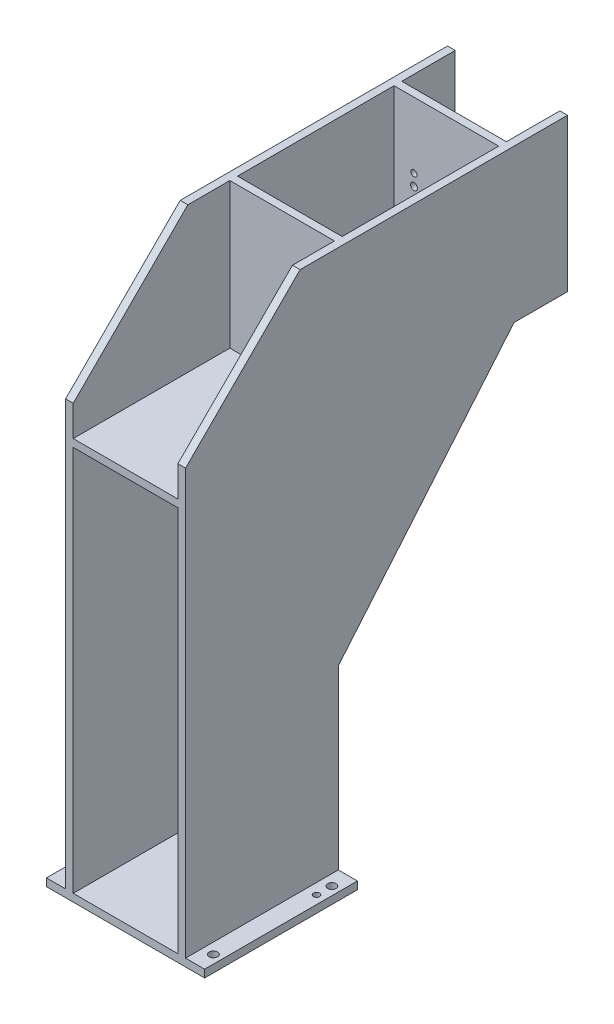
SolidWorks part; units mm, degrees
material "1.0736 (11SMn37)"
ref_plane "Front Plane" through (0, 0, 0) normal (0, 0, 1) x (1, 0, 0)
ref_plane "Top Plane" through (0, 0, 0) normal (0, 1, 0) x (1, 0, 0)
ref_plane "Right Plane" through (0, 0, 0) normal (1, 0, 0) x (0, 0, -1)
sketch "Sketch1" plane through (0, 0, 0) normal (1, 0, 0) x (0, 0, -1)
  line L0 (0, 0) -> (0, 565.5)
  line L1 (0, 565.5) -> (150, 715.5)
  line L2 (150, 715.5) -> (500, 715.5)
  line L3 (500, 715.5) -> (500, 515.5)
  line L6 (200, 0) -> (0, 0)
  line L11 (200, 0) -> (200, 515.5)
  line L12 (200, 515.5) -> (500, 515.5)
  line L13 (200, 241.3967) -> (430, 515.5)
  dimension "D1" = 200
  dimension "D2" = 715.5
  dimension "D3" = 565.5
  dimension "D4" = 200
  dimension "D5" = 500
  dimension "D6" = 45
  dimension "D7" = 40
  dimension "D8" = 230
extrude "Boss-Extrude1" add sketch "Sketch1" along normal blind 10 and the other way blind 147 contours L11 L13 L12 | L11 L12 L3 L2 L1 L0 L6
sketch "Sketch3" plane through (0, 715.5, 0) normal (0, 1, 0) x (1, 0, 0)
  line L0 (-147, 500) -> (10, 500) construction
  line L1 (-137, 500) -> (0, 500)
  line L2 (-137, 500) -> (-137, 0)
  line L3 (-137, 0) -> (0, 0)
  line L4 (0, 500) -> (0, 0)
  line L5 (-147, 0) -> (10, 0) construction
  point P8 (-68.5, 500)
  point P9 (-68.5, 500)
  dimension "D1" = 137
extrude "Cut-Extrude1" cut sketch "Sketch3" against normal offset from surface (705.5 mm away) 10 up to face at (-68.5, 0, -100)
ref_plane "Plane1" through (0, 0, -430) normal (0, 0, -1) x (-1, 0, 0)
sketch "Sketch4" plane through (0, 0, -430) normal (0, 0, -1) x (-1, 0, 0)
  line L1 (0, 715.5) -> (137, 715.5)
  line L2 (0, 715.5) -> (0, 515.5)
  line L3 (0, 515.5) -> (137, 515.5)
  line L4 (137, 715.5) -> (137, 515.5)
extrude "Boss-Extrude2" add sketch "Sketch4" against normal blind 10 contours L2 L1 L4 L3
sketch "Sketch6" plane through (0, 0, -420) normal (0, 0, 1) x (1, 0, 0)
  line L0 (0, 515.5) -> (-137, 515.5) construction
  line L1 (-111, 567.7) -> (-26, 567.7) construction
  line L2 (0, 715.5) -> (-137, 715.5) construction
  line L3 (0, 715.5) -> (0, 515.5) construction
  circle A0 centre (-111, 567.7) radius 4.5
  circle A1 centre (-26, 567.7) radius 4.5
  circle A2 centre (-111, 614.2) radius 4.5
  circle A3 centre (-26, 614.2) radius 4.5
  circle A4 centre (-63, 609) radius 8
  circle A5 centre (-111, 629.2) radius 4
  circle A6 centre (-26, 552.7) radius 4
  circle A7 centre (-111, 590.7) radius 4.5
  circle A8 centre (-26, 590.7) radius 4.5
  point P10 (-68.5, 715.5)
  point P11 (-68.5, 567.7)
  dimension "D3" = 9
  dimension "D5" = 16
  dimension "D8" = 8
  dimension "D1" = 52.2
  dimension "D2" = 85
  dimension "D4" = 46.5
  dimension "D6" = 93.5
  dimension "D7" = 63
  dimension "D9" = 15
  dimension "D10" = 15
  dimension "D11" = 23
extrude "Cut-Extrude3" cut sketch "Sketch6" against normal up to next
ref_plane "Plane2" through (0, 525.5, 0) normal (0, -1, 0) x (-1, 0, 0)
sketch "Sketch9" plane through (0, 0, 0) normal (0, -1, 0) x (1, 0, 0)
  line L1 (-147, -200) -> (-172, -200)
  line L2 (-147, -200) -> (-147, 0)
  line L3 (-147, 0) -> (-172, 0)
  line L4 (-172, -200) -> (-172, 0)
  line L5 (10, -200) -> (35, -200)
  line L6 (10, -200) -> (10, 0)
  line L7 (10, 0) -> (35, 0)
  line L8 (35, -200) -> (35, 0)
  dimension "D1" = 200
  dimension "D2" = 200
  dimension "D3" = 25
  dimension "D4" = 25
extrude "Boss-Extrude4" add sketch "Sketch9" against normal blind 10
sketch "Sketch10" plane through (0, 0, 0) normal (0, -1, 0) x (1, 0, 0)
  line L0 (-161, -22.5) -> (24, -22.5) construction
  line L1 (24, -22.5) -> (24, -177.5) construction
  line L2 (24, -177.5) -> (-161, -177.5) construction
  line L3 (-161, -177.5) -> (-161, -22.5) construction
  line L4 (-172, 0) -> (35, 0) construction
  line L6 (-172, 0) -> (-172, -200) construction
  circle A0 centre (-161, -22.5) radius 5.5
  circle A1 centre (24, -22.5) radius 5.5
  circle A2 centre (24, -177.5) radius 5.5
  circle A3 centre (-161, -177.5) radius 5.5
  circle A4 centre (-161, -42.5) radius 4
  circle A5 centre (24, -157.5) radius 4
  point P6 (-68.5, 0)
  point P7 (-68.5, -22.5)
  point P10 (-172, -100)
  point P11 (-161, -100)
  dimension "D3" = 11
  dimension "D4" = 8
  dimension "D1" = 185
  dimension "D2" = 155
  dimension "D5" = 20
  dimension "D6" = 20
extrude "Cut-Extrude4" cut sketch "Sketch10" against normal through all
sketch "Sketch11" plane through (0, 515.5, 0) normal (0, -1, 0) x (1, 0, 0)
  line L1 (-137, -430) -> (0, -430)
  line L2 (-137, -430) -> (-137, 0)
  line L3 (-137, 0) -> (0, 0)
  line L4 (0, -430) -> (0, 0)
extrude "Boss-Extrude5" add sketch "Sketch11" against normal blind 10
sketch "Sketch12" plane through (-137, 0, 0) normal (1, 0, 0) x (0, 0, -1)
  line L0 (150, 715.5) -> (500, 715.5) construction
  line L1 (205, 715.5) -> (215, 715.5)
  line L2 (205, 715.5) -> (205, 515.5)
  line L3 (205, 515.5) -> (215, 515.5)
  line L4 (215, 715.5) -> (215, 515.5)
  dimension "D1" = 10
  dimension "D2" = 200
  dimension "D3" = 55
extrude "Boss-Extrude6" add sketch "Sketch12" along normal up to surface (137 mm away) up to face at (0, 609.5, -198)
ref_plane "Plane4" through (0, 262.75, 0) normal (0, 1, 0) x (1, 0, 0)
